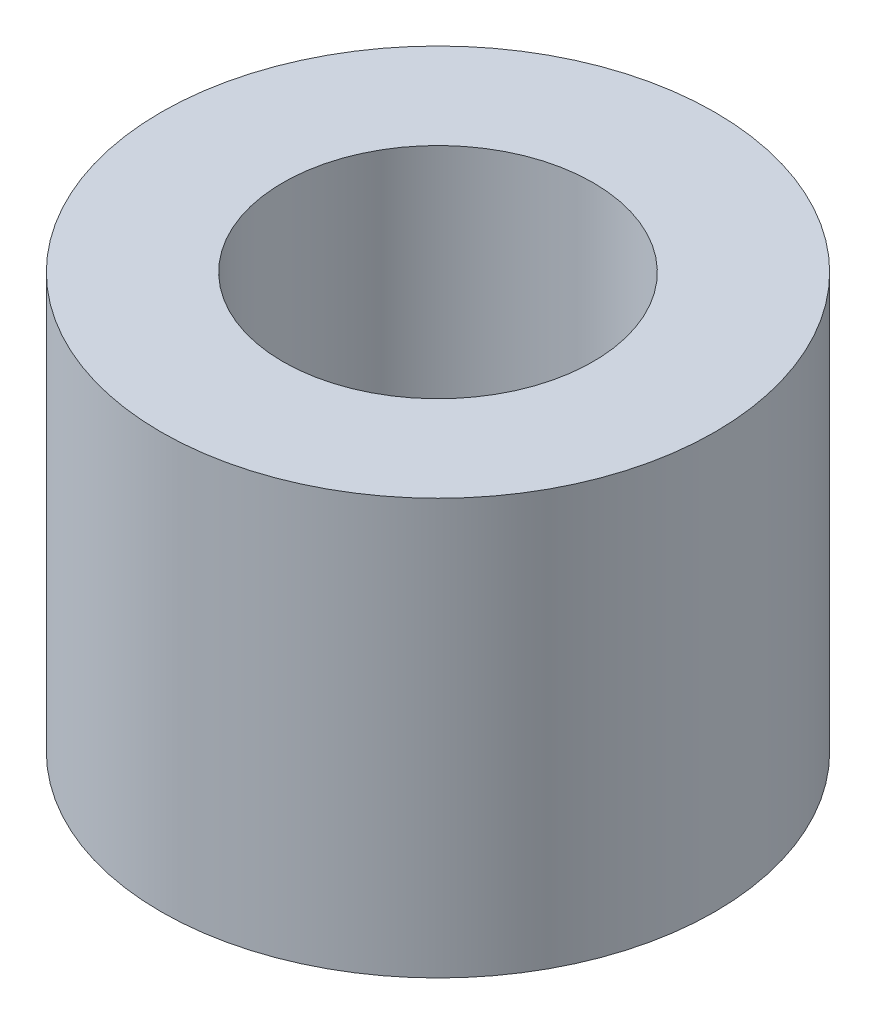
SolidWorks part; units mm, degrees
ref_plane "Front Plane" through (0, 0, 0) normal (0, 0, 1) x (1, 0, 0)
ref_plane "Top Plane" through (0, 0, 0) normal (0, 1, 0) x (1, 0, 0)
ref_plane "Right Plane" through (0, 0, 0) normal (1, 0, 0) x (0, 0, -1)
sketch "Sketch1" plane through (0, 0, 0) normal (0, 1, 0) x (1, 0, 0)
  circle A0 centre (0, 0) radius 3.175
  dimension "D1" = 6.35
extrude "Boss-Extrude1" add sketch "Sketch1" along normal blind 4.7625
hole_wizard "#6 Clearance Hole1" positions "Sketch3" profile "Sketch2" hole size "#6" standard "Ansi Inch"
sketch "Sketch3" plane through (0, 4.7625, 0) normal (0, 1, 0) x (-1, 0, 0)
  circle A0 centre (0, 0) radius 3.175 construction
  point P0 (0, 0)
sketch "Sketch2" plane through (0, 4.7625, 0) normal (1, 0, 0) x (0, 0, 1)
  line L0 (0, 0) -> (0, 8.6883)
  line L1 (0, 8.6883) -> (1.778, 7.62)
  line L2 (1.778, 7.62) -> (1.778, 0)
  line L5 (1.778, 0) -> (0, 0)
  line L10 (0, 8.6883) -> (-1.778, 7.62) construction
  line L11 (0, -6.35) -> (0, 107.95) construction
  dimension "Hole Dia." = 3.556
  dimension "Hole Depth" = 7.62
  dimension "Drill Angle" = 118
